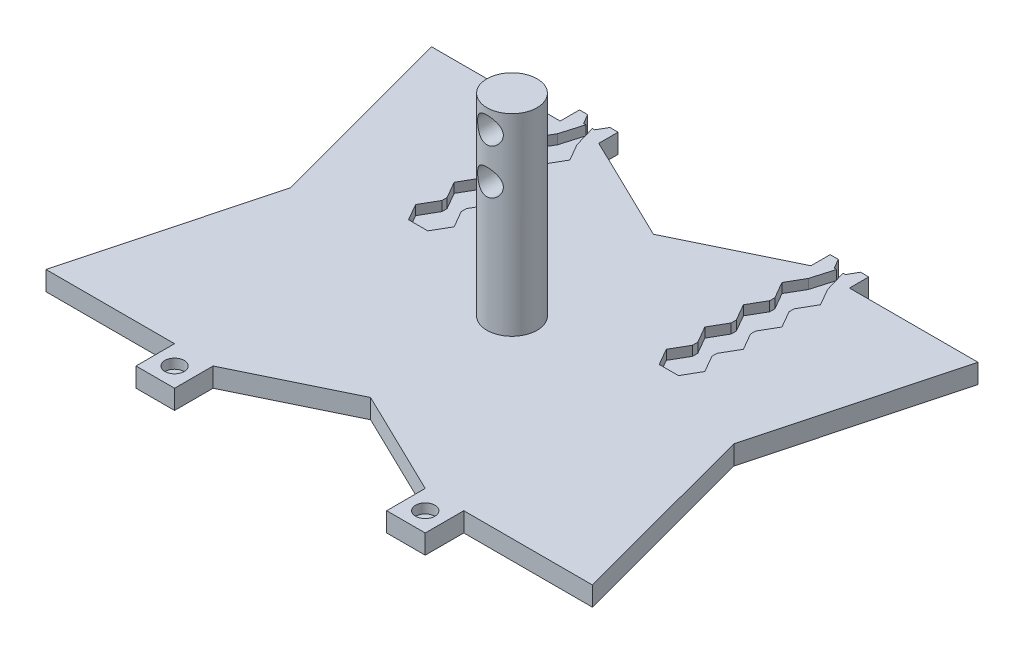
SolidWorks part; units mm, degrees
ref_plane "Alzado" through (0, 0, 0) normal (0, 0, 1) x (1, 0, 0)
ref_plane "Planta" through (0, 0, 0) normal (0, 1, 0) x (1, 0, 0)
ref_plane "Vista lateral" through (0, 0, 0) normal (1, 0, 0) x (0, 0, -1)
sketch "Croquis1" plane through (0, 0, 0) normal (0, 1, 0) x (1, 0, 0)
  line L0 (30, 60) -> (30, 63)
  line L1 (0, 0) -> (30, 0) construction
  line L2 (0, 0) -> (0, 60) construction
  line L3 (0, 60) -> (30, 60) construction
  line L4 (30, 63) -> (36, 63) construction
  line L5 (36, 63) -> (36, 60)
  line L6 (36, 60) -> (69, 60) construction
  line L7 (69, 60) -> (69, 63)
  line L8 (69, 63) -> (75, 63) construction
  line L9 (75, 63) -> (75, 60)
  line L10 (75, 60) -> (105, 60) construction
  line L11 (105, 60) -> (105, 0) construction
  line L12 (105, 0) -> (75, 0) construction
  line L13 (75, 0) -> (75, -6)
  line L14 (30, -6) -> (36, -6)
  line L15 (69, -6) -> (69, 0)
  line L16 (69, 0) -> (36, 0) construction
  line L17 (36, 0) -> (36, -6)
  line L18 (69, -6) -> (75, -6)
  line L19 (30, -6) -> (30, 0)
  line L20 (30, 60) -> (36, 60) construction
  line L21 (69, 60) -> (75, 60) construction
  line L22 (30, 0) -> (36, 0) construction
  line L23 (69, 0) -> (75, 0) construction
  line L24 (30, 63) -> (31.2679, 63)
  line L25 (34.7321, 63) -> (36, 63)
  line L26 (33.866, 61.5) -> (34.7321, 63)
  line L27 (34.7321, 63) -> (33.866, 64.5) construction
  line L28 (33.866, 64.5) -> (32.134, 64.5) construction
  line L29 (32.134, 64.5) -> (31.2679, 63) construction
  line L30 (31.2679, 63) -> (32.134, 61.5)
  line L31 (32.134, 61.5) -> (33.866, 61.5)
  line L32 (73.7321, 63) -> (72.866, 64.5) construction
  line L33 (72.866, 64.5) -> (71.134, 64.5) construction
  line L34 (71.134, 64.5) -> (70.2679, 63) construction
  line L35 (70.2679, 63) -> (71.134, 61.5)
  line L36 (71.134, 61.5) -> (72.866, 61.5)
  line L37 (72.866, 61.5) -> (73.7321, 63)
  line L38 (33, 0) -> (33, -6) construction
  line L39 (72, 0) -> (72, -6) construction
  line L40 (30, 60) -> (10, 60)
  line L41 (10, 60) -> (18, 30)
  line L42 (18, 30) -> (10, 0)
  line L43 (10, 0) -> (30, 0)
  line L44 (75, 60) -> (95, 60)
  line L45 (95, 60) -> (87, 30)
  line L46 (87, 30) -> (95, 0)
  line L47 (95, 0) -> (75, 0)
  line L48 (18, 30) -> (0, 30) construction
  line L49 (87, 30) -> (105, 30) construction
  line L50 (69, 63) -> (70.2679, 63)
  line L51 (73.7321, 63) -> (75, 63)
  line L52 (36, 60) -> (52.5, 52)
  line L53 (52.5, 52) -> (69, 60)
  line L54 (69, 0) -> (52.5, 8)
  line L55 (52.5, 8) -> (36, 0)
  line L56 (52.5, 52) -> (52.5, 60) construction
  line L57 (52.5, 8) -> (52.5, 0) construction
  line L58 (75, 60) -> (75, 0) construction
  line L59 (30, 0) -> (30, 60) construction
  line L68 (92.4667, 58) -> (94.4667, 58) construction
  circle A0 centre (33, 63) radius 1.5 construction
  circle A1 centre (72, 63) radius 1.5 construction
  circle A2 centre (33, -3) radius 0.5
  circle A3 centre (72, -3) radius 0.5
  dimension "D6" = 3
  dimension "D7" = 1
  dimension "D1" = 60
  dimension "D2" = 30
  dimension "D3" = 45
  dimension "D4" = 6
  dimension "D5" = 3
  dimension "D8" = 8
  dimension "D9" = 10
  dimension "D10" = 8
extrude "Saliente-Extruir1" add sketch "Croquis1" along normal blind 3
sketch "Croquis2" plane through (0, 3, 0) normal (0, 1, 0) x (1, 0, 0)
  line L0 (18, 30) -> (87, 30) construction
  circle A0 centre (52.5, 30) radius 3.9
  dimension "D1" = 7.8
extrude "Saliente-Extruir2" add sketch "Croquis2" along normal blind 30
sketch "Croquis3" plane through (0, 0, 0) normal (0, 0, 1) x (1, 0, 0)
  line L0 (10, 0) -> (95, 0) construction
  line L1 (52.5, 0) -> (52.5, 23) construction
  line L2 (52.5, 23) -> (52.5, 30) construction
  circle A0 centre (52.5, 30) radius 2
  circle A1 centre (52.5, 23) radius 2
  dimension "D1" = 4
  dimension "D2" = 7
  dimension "D3" = 30
extrude "Cortar-Extruir1" cut sketch "Croquis3" against normal through all
sketch "Croquis4" plane through (0, 3, 0) normal (0, 1, 0) x (1, 0, 0)
  circle A0 centre (33, -3) radius 1.5
  circle A1 centre (72, -3) radius 1.5
  dimension "D1" = 3
extrude "Cortar-Extruir2" cut sketch "Croquis4" against normal blind 1.5
sketch "Croquis5" plane through (0, 3, 0) normal (0, 1, 0) x (1, 0, 0)
  line L0 (33, 61.5) -> (33, 55.5) construction
  line L1 (33, 55.5) -> (33, 49.5) construction
  line L2 (32.5, 61.5) -> (33.5, 61.5)
  line L3 (33.866, 61.5) -> (32.134, 61.5) construction
  line L4 (33, 49.5) -> (33, 43.5) construction
  line L5 (33, 43.5) -> (33, 37.5) construction
  line L6 (31.5, 58.0981) -> (32.5, 61.5)
  line L7 (34.5, 58.0981) -> (31.5, 58.0981) construction
  line L8 (31.5, 58.0981) -> (30, 55.5)
  line L9 (30, 55.5) -> (31.5, 52.9019)
  line L10 (31.5, 52.9019) -> (34.5, 52.9019) construction
  line L11 (34.5, 52.9019) -> (36, 55.5)
  line L12 (36, 55.5) -> (34.5, 58.0981)
  line L13 (36, 49.5) -> (34.5, 52.0981)
  line L14 (34.5, 52.0981) -> (31.5, 52.0981) construction
  line L15 (31.5, 52.0981) -> (30, 49.5)
  line L16 (30, 49.5) -> (31.5, 46.9019)
  line L17 (31.5, 46.9019) -> (34.5, 46.9019) construction
  line L18 (34.5, 46.9019) -> (36, 49.5)
  line L19 (36, 43.5) -> (34.5, 46.0981)
  line L20 (34.5, 46.0981) -> (31.5, 46.0981) construction
  line L21 (33.5, 61.5) -> (34.5, 58.0981)
  line L22 (31.5, 46.0981) -> (30, 43.5)
  line L23 (30, 43.5) -> (31.5, 40.9019)
  line L24 (31.5, 40.9019) -> (34.5, 40.9019) construction
  line L25 (34.5, 40.9019) -> (36, 43.5)
  line L26 (36, 37.5) -> (34.5, 40.0981)
  line L27 (34.5, 40.0981) -> (31.5, 40.0981) construction
  line L28 (31.5, 40.0981) -> (30, 37.5)
  line L29 (30, 37.5) -> (31.5, 34.9019)
  line L30 (31.5, 34.9019) -> (34.5, 34.9019)
  line L31 (34.5, 34.9019) -> (36, 37.5)
  line L32 (31.5, 52.9019) -> (31.5, 52.0981)
  line L33 (34.5, 52.9019) -> (34.5, 52.0981)
  line L34 (34.5, 46.9019) -> (34.5, 46.0981)
  line L35 (31.5, 46.9019) -> (31.5, 46.0981)
  line L36 (31.5, 40.9019) -> (31.5, 40.0981)
  line L37 (34.5, 40.9019) -> (34.5, 40.0981)
  line L38 (72, 61.5) -> (72, 55.5) construction
  line L39 (72.866, 61.5) -> (71.134, 61.5) construction
  line L40 (72, 55.5) -> (72, 49.5) construction
  line L41 (72, 49.5) -> (72, 43.5) construction
  line L42 (72, 43.5) -> (72, 37.5) construction
  line L43 (71.5, 61.5) -> (70.5, 58.0981)
  line L44 (75, 55.5) -> (73.5, 58.0981)
  line L45 (73.5, 58.0981) -> (70.5, 58.0981) construction
  line L46 (70.5, 58.0981) -> (69, 55.5)
  line L47 (69, 55.5) -> (70.5, 52.9019)
  line L48 (70.5, 52.9019) -> (73.5, 52.9019) construction
  line L49 (73.5, 52.9019) -> (75, 55.5)
  line L50 (75, 49.5) -> (73.5, 52.0981)
  line L51 (73.5, 52.0981) -> (70.5, 52.0981) construction
  line L52 (70.5, 52.0981) -> (69, 49.5)
  line L53 (69, 49.5) -> (70.5, 46.9019)
  line L54 (70.5, 46.9019) -> (73.5, 46.9019) construction
  line L55 (73.5, 46.9019) -> (75, 49.5)
  line L56 (75, 43.5) -> (73.5, 46.0981)
  line L57 (73.5, 46.0981) -> (70.5, 46.0981) construction
  line L58 (70.5, 46.0981) -> (69, 43.5)
  line L59 (69, 43.5) -> (70.5, 40.9019)
  line L60 (70.5, 40.9019) -> (73.5, 40.9019) construction
  line L61 (73.5, 40.9019) -> (75, 43.5)
  line L62 (75, 37.5) -> (73.5, 40.0981)
  line L63 (73.5, 40.0981) -> (70.5, 40.0981) construction
  line L64 (70.5, 40.0981) -> (69, 37.5)
  line L65 (69, 37.5) -> (70.5, 34.9019)
  line L66 (70.5, 34.9019) -> (73.5, 34.9019)
  line L67 (73.5, 34.9019) -> (75, 37.5)
  line L68 (70.5, 52.9019) -> (70.5, 52.0981)
  line L69 (70.5, 46.9019) -> (70.5, 46.0981)
  line L70 (70.5, 40.9019) -> (70.5, 40.0981)
  line L71 (73.5, 40.0981) -> (73.5, 40.9019)
  line L72 (73.5, 46.0981) -> (73.5, 46.9019)
  line L73 (73.5, 52.0981) -> (73.5, 52.9019)
  line L74 (73.5, 58.0981) -> (72.5, 61.5)
  line L75 (71.5, 61.5) -> (72.5, 61.5)
  circle A0 centre (33, 55.5) radius 2.5981 construction
  circle A1 centre (33, 49.5) radius 2.5981 construction
  circle A2 centre (33, 43.5) radius 2.5981 construction
  circle A3 centre (33, 37.5) radius 2.5981 construction
  circle A4 centre (72, 55.5) radius 2.5981 construction
  circle A5 centre (72, 49.5) radius 2.5981 construction
  circle A6 centre (72, 43.5) radius 2.5981 construction
  circle A7 centre (72, 37.5) radius 2.5981 construction
  point P7 (33, 61.5)
  point P74 (72, 61.5)
  dimension "D1" = 3
  dimension "D2" = 6
  dimension "D3" = 1
extrude "Cortar-Extruir3" cut sketch "Croquis5" against normal blind 1.5
